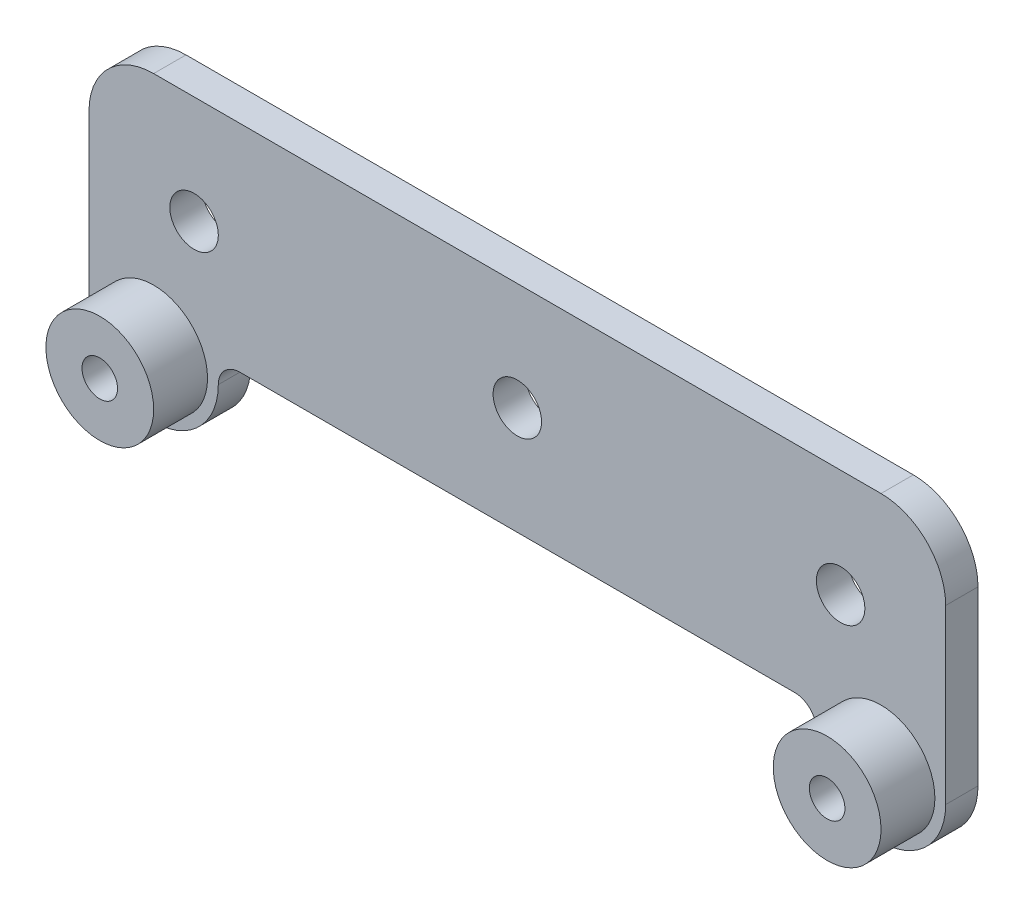
SolidWorks part; units mm, degrees
material "ABS"
ref_plane "前基準面" through (0, 0, 0) normal (0, 0, 1) x (1, 0, 0)
ref_plane "上基準面" through (0, 0, 0) normal (0, 1, 0) x (1, 0, 0)
ref_plane "右基準面" through (0, 0, 0) normal (1, 0, 0) x (0, 0, -1)
sketch "草圖1" plane through (0, 0, 0) normal (0, 0, 1) x (1, 0, 0)
  line L0 (-33.75, 10) -> (33.75, 10)
  line L5 (39.75, 4) -> (39.75, -12)
  line L8 (25.75, -10) -> (-25.75, -10)
  line L11 (-39.75, -12) -> (-39.75, 4)
  line L12 (0, -10) -> (0, 10) construction
  line L13 (-33.75, -12) -> (33.75, -12) construction
  arc A0 (-39.75, -12) -> (-27.75, -12) centre (-33.75, -12) ccw
  arc A1 (27.75, -12) -> (39.75, -12) centre (33.75, -12) ccw
  arc A2 (33.75, 10) -> (39.75, 4) centre (33.75, 4) cw
  arc A3 (-33.75, 10) -> (-39.75, 4) centre (-33.75, 4) ccw
  arc A4 (27.75, -12) -> (25.75, -10) centre (25.75, -12) ccw
  arc A5 (-25.75, -10) -> (-27.75, -12) centre (-25.75, -12) ccw
  dimension "D3" = 6
  dimension "D1" = 20
  dimension "D2" = 67.5
  dimension "D4" = 12
extrude "填料-伸長1" add sketch "草圖1" along normal blind 3
sketch "草圖4" plane through (0, 0, 3) normal (0, 0, 1) x (1, 0, 0)
  circle A0 centre (-33.75, -12) radius 5
  circle A1 centre (33.75, -12) radius 5
  dimension "D1" = 10
extrude "填料-伸長2" add sketch "草圖4" along normal blind 5
hole_wizard "M4x0.7 螺紋孔1" positions "草圖5" profile "草圖6" tap size "M4x0.7" standard "Ansi Metric" end condition through all
sketch "草圖5" plane through (0, 0, 8) normal (0, 0, 1) x (1, 0, 0)
  point P0 (-33.75, -12)
  point P3 (33.75, -12)
sketch "草圖6" plane through (-33.75, -12, 8) normal (1, 0, 0) x (0, -1, 0)
  line L0 (0, 0) -> (0, 8)
  line L1 (0, 8) -> (1.65, 8)
  line L2 (1.65, 8) -> (1.65, 0)
  line L5 (1.65, 0) -> (0, 0)
  line L11 (0, -6.35) -> (0, 107.95) construction
  dimension "貫穿螺孔鑽直徑" = 3.3
  dimension "貫穿螺孔鑽深度" = 8
hole_wizard "M4 餘隙孔1" positions "草圖7" profile "草圖8" hole size "M4" standard "Ansi Metric" end condition through all
sketch "草圖7" plane through (0, 0, 3) normal (0, 0, 1) x (1, 0, 0)
  line L0 (-30, 0) -> (30, 0) construction
  point P1 (-30, 0)
  point P2 (30, 0)
  point P10 (0, 0)
  dimension "D1" = 60
sketch "草圖8" plane through (-30, 0, 3) normal (1, 0, 0) x (0, -1, 0)
  line L0 (0, 0) -> (0, 3)
  line L1 (0, 3) -> (2.25, 3)
  line L2 (2.25, 3) -> (2.25, 0)
  line L5 (2.25, 0) -> (0, 0)
  line L11 (0, -6.35) -> (0, 107.95) construction
  dimension "貫穿孔直徑" = 4.5
  dimension "貫穿孔深度" = 3
equation "\"ˇ\"=3"
